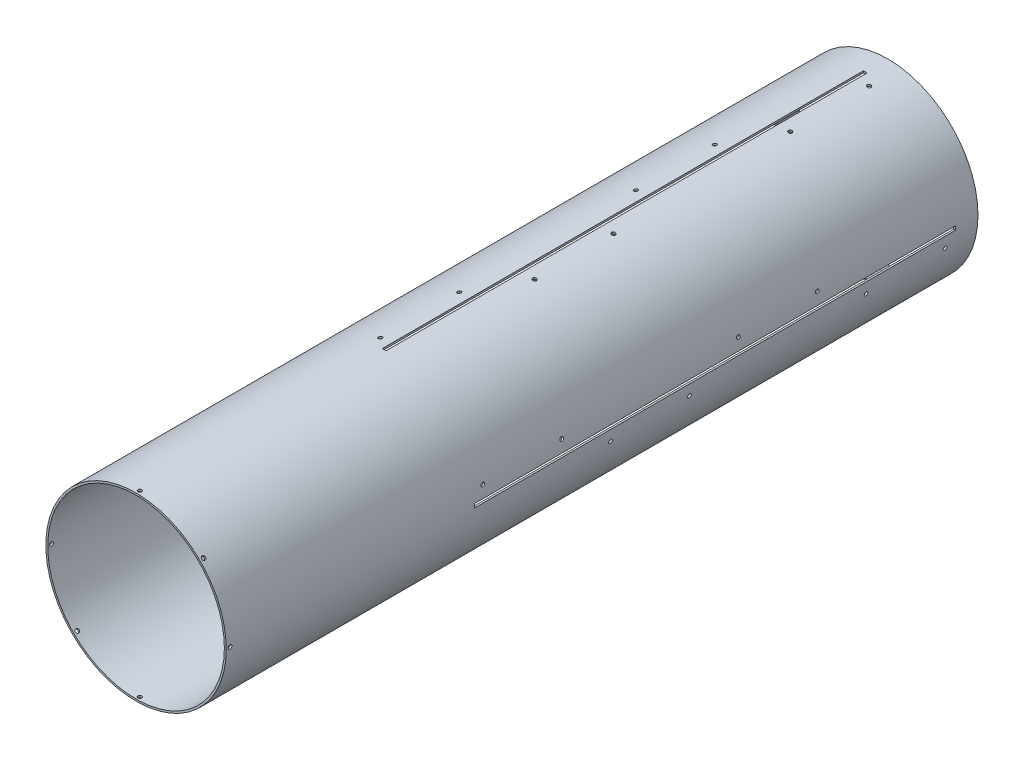
SolidWorks part; units mm, degrees
material "6061-T6 (SS)"
ref_plane "Front Plane" through (0, 0, 0) normal (0, 0, 1) x (1, 0, 0)
ref_plane "Top Plane" through (0, 0, 0) normal (0, 1, 0) x (1, 0, 0)
ref_plane "Right Plane" through (0, 0, 0) normal (1, 0, 0) x (0, 0, -1)
sketch "Sketch1" plane through (0, 0, 0) normal (0, 0, 1) x (1, 0, 0)
  circle A0 centre (0, 0) radius 152.4
  dimension "D1" = 304.8
extrude "Boss-Extrude1" add sketch "Sketch1" along normal blind 1270 contours A0
ref_plane "Plane2" [suppressed] through (19.6284, -151.1307, 0) normal (0.1288, -0.9917, 0) x (0, 0, -1)
ref_plane "Plane1" [suppressed] through (-19.6284, -151.1307, 0) normal (-0.1288, -0.9917, 0) x (0, 0, -1)
sketch "Sketch2" plane through (0, 0, 1270) normal (0, 0, 1) x (1, 0, 0)
  circle A0 centre (0, 0) radius 149.225
  dimension "D1" = 298.45
extrude "Cut-Extrude1" cut sketch "Sketch2" against normal blind 1270 contours A0
sketch "Sketch3" plane through (0, 0, 0) normal (0, 1, 0) x (1, 0, 0)
  line L0 (0, 0) -> (0, -25.4) construction
sketch "Sketch4" plane through (0, 0, 0) normal (0, 1, 0) x (1, 0, 0)
  line L1 (-152.4, -1270) -> (152.4, -1270) construction
  line L2 (0, -1270) -> (0, -1263.65) construction
  circle A0 centre (0, -1263.65) radius 3.175
  dimension "D1" = 6.35
  dimension "D2" = 6.35
extrude "Cut-Extrude2" cut sketch "Sketch4" against normal blind 300.482
pattern_circular "CirPattern1" count 8 over 360 about axis through (0, 0, 1270) along (0, 0, 1) of "Cut-Extrude2"
sketch "Sketch6" plane through (0, 0, 0) normal (0, 1, 0) x (1, 0, 0)
  line L1 (-3.175, -850.9) -> (3.175, -850.9)
  line L3 (-3.175, -38.1) -> (3.175, -38.1)
  line L4 (3.175, -850.9) -> (3.175, -38.1)
  line L5 (152.4, 0) -> (-152.4, 0) construction
  line L6 (0, -25.4) -> (0, -850.9) construction
  line L7 (-3.175, -850.9) -> (-3.175, -38.1)
  point P11 (0, -38.1)
  dimension "D2" = 6.35
  dimension "D3" = 38.1
  dimension "D1" = 812.8
extrude "Cut-Extrude3" cut sketch "Sketch6" against normal blind 152.4
pattern_circular "CirPattern2" count 4 over 360 about axis through (0, 0, 0) along (0, 0, 1) of "Cut-Extrude3"
sketch "Sketch7" plane through (-20.3677, 146.788, 850.9) normal (-0.1383, 0.9904, 0) x (0.9904, 0.1383, 0)
  circle A0 centre (-1.4845, 149.225) radius 3.175 construction
  circle A1 centre (-1.4845, 15.875) radius 3.175 construction
  circle A2 centre (-1.4845, 149.225) radius 3.175
  circle A3 centre (-1.4845, 15.875) radius 3.175
  circle A4 centre (-1.4845, 447.675) radius 3.175 construction
  circle A5 centre (-1.4845, 581.025) radius 3.175 construction
  circle A6 centre (-1.4845, 447.675) radius 3.175
  circle A7 centre (-1.4845, 581.025) radius 3.175
extrude "Cut-Extrude4" cut sketch "Sketch7" along normal up to surface (4.1383 mm away)
sketch "Sketch8" plane through (20.3677, 146.788, 469.9) normal (0.1383, 0.9904, 0) x (-0.9904, 0.1383, 0)
  circle A0 centre (-1.4845, -282.575) radius 3.175 construction
  circle A1 centre (-1.4845, -415.925) radius 3.175 construction
  circle A2 centre (-1.4845, 15.875) radius 3.175 construction
  circle A3 centre (-1.4845, 149.225) radius 3.175 construction
  circle A4 centre (-1.4845, -282.575) radius 3.175
  circle A5 centre (-1.4845, -415.925) radius 3.175
  circle A6 centre (-1.4845, 15.875) radius 3.175
  circle A7 centre (-1.4845, 149.225) radius 3.175
extrude "Cut-Extrude5" cut sketch "Sketch8" along normal up to surface (4.1949 mm away)
pattern_circular "CirPattern3" count 4 over 360 about axis through (0, 0, 0) along (0, 0, 1) of "Cut-Extrude5", "Cut-Extrude4"
equation "\"Rocket Diameter\"= 12in"
equation "\"D1@Sketch1\"=\"Rocket Diameter\""
equation "\"Airframe Thickness\"= 0.125in"
equation "\"Length\"= 50in"
equation "\"D1@Boss-Extrude1\"=\"Length\""
equation "\"D1@Cut-Extrude1\"=\"Length\""
equation "\"Bolt Diameter\"= 0.25in"
equation "\"D1@Sketch2\"= \"Rocket Diameter\"-\"Airframe Thickness\"*2"
equation "\"D1@Sketch4\"=\"Bolt Diameter\""
equation "\"Fin Root Chord\"= 32in"
equation "\"Fin Thickness\"= .25in"
equation "\"D2@Sketch6\"=\"Fin Thickness\""
equation "\"D1@Sketch6\"=\"Fin Root Chord\""
